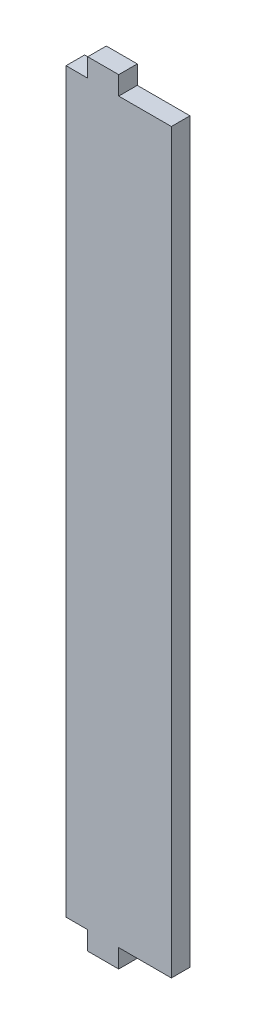
SolidWorks part; units mm, degrees
ref_plane "Plan de face" through (0, 0, 0) normal (0, 0, 1) x (1, 0, 0)
ref_plane "Plan de dessus" through (0, 0, 0) normal (0, 1, 0) x (1, 0, 0)
ref_plane "Plan de droite" through (0, 0, 0) normal (1, 0, 0) x (0, 0, -1)
sketch "Esquisse1" plane through (0, 0, 0) normal (0, 0, 1) x (1, 0, 0)
  line L1 (-17, 119) -> (17, 119)
  line L2 (-17, 119) -> (-17, -119)
  line L3 (-17, -119) -> (17, -119)
  line L4 (17, 119) -> (17, -119)
  point P7 (-1.2728, 115.3581)
  dimension "D1" = 238
  dimension "D2" = 34
  dimension "D3" = 17
  dimension "D4" = 119
extrude "Boss.-Extru.1" add sketch "Esquisse1" along normal blind 6
sketch "Esquisse2" plane through (0, 0, 6) normal (0, 0, 1) x (1, 0, 0)
  line L0 (17, 119) -> (-17, 119) construction
  line L1 (-10, 119) -> (0, 119)
  line L2 (-10, 119) -> (-10, 125)
  line L3 (-10, 125) -> (0, 125)
  line L4 (0, 119) -> (0, 125)
  line L5 (79.5873, 0) -> (-118.1919, 0) construction
  line L6 (-17, 119) -> (-17, -119) construction
  line L7 (0, -119) -> (0, -125)
  line L8 (-10, -125) -> (0, -125)
  line L9 (-10, -119) -> (-10, -125)
  line L10 (-10, -119) -> (0, -119)
  dimension "D1" = 10
  dimension "D2" = 6
  dimension "D3" = 7
extrude "Boss.-Extru.2" add sketch "Esquisse2" against normal blind 6
